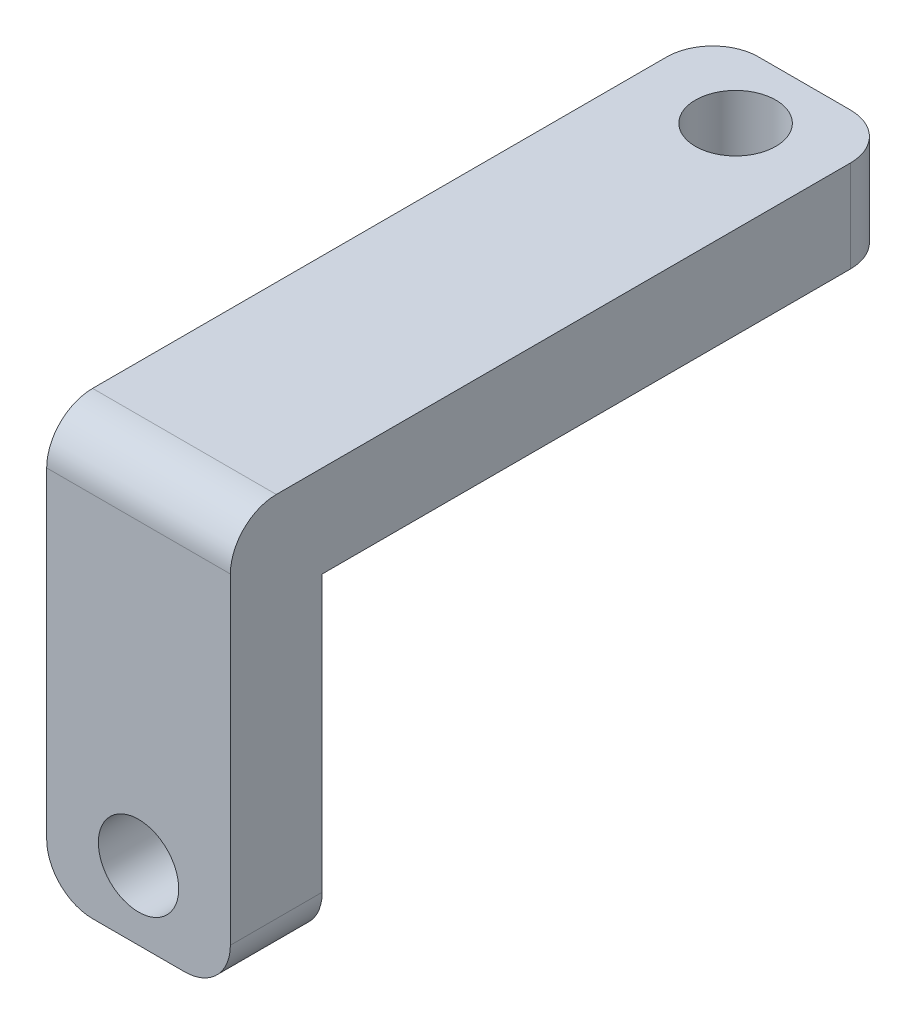
SolidWorks part; units mm, degrees
ref_plane "Plan de face" through (0, 0, 0) normal (0, 0, 1) x (1, 0, 0)
ref_plane "Plan de dessus" through (0, 0, 0) normal (0, 1, 0) x (1, 0, 0)
ref_plane "Plan de droite" through (0, 0, 0) normal (1, 0, 0) x (0, 0, -1)
sketch "Esquisse1" plane through (0, 0, 0) normal (0, 1, 0) x (1, 0, 0)
  line L1 (-4, 12.5) -> (4, 12.5)
  line L2 (-4, 12.5) -> (-4, -12.5)
  line L3 (-4, -12.5) -> (4, -12.5)
  line L4 (4, 12.5) -> (4, -12.5)
  circle A0 centre (0, 9.5) radius 1.75
  point P4 (0, 12.5)
  point P5 (-4, 0)
  dimension "D2" = 3
  dimension "D3" = 3.5
  dimension "D1" = 25
  dimension "D4" = 8
extrude "Boss.-Extru.1" add sketch "Esquisse1" along normal blind 4
sketch "Esquisse2" plane through (0, 0, 12.5) normal (0, 0, 1) x (1, 0, 0)
  line L0 (4, 4) -> (4, 0) construction
  line L1 (-4, 4) -> (4, 4)
  line L2 (-4, 4) -> (-4, -14)
  line L3 (-4, -14) -> (4, -14)
  line L4 (4, 4) -> (4, -14)
  line L5 (-4, 4) -> (4, 4) construction
  circle A0 centre (0, -11) radius 1.75
  dimension "D1" = 3.5
  dimension "D2" = 15
  dimension "D3" = 18
extrude "Boss.-Extru.2" add sketch "Esquisse2" along normal blind 4
fillet "Congé1" radius 2 5 edges at (4, -14, 14.5) (-4, -14, 14.5) (-4, 2, -12.5) (4, 2, -12.5) (0, 4, 16.5)
